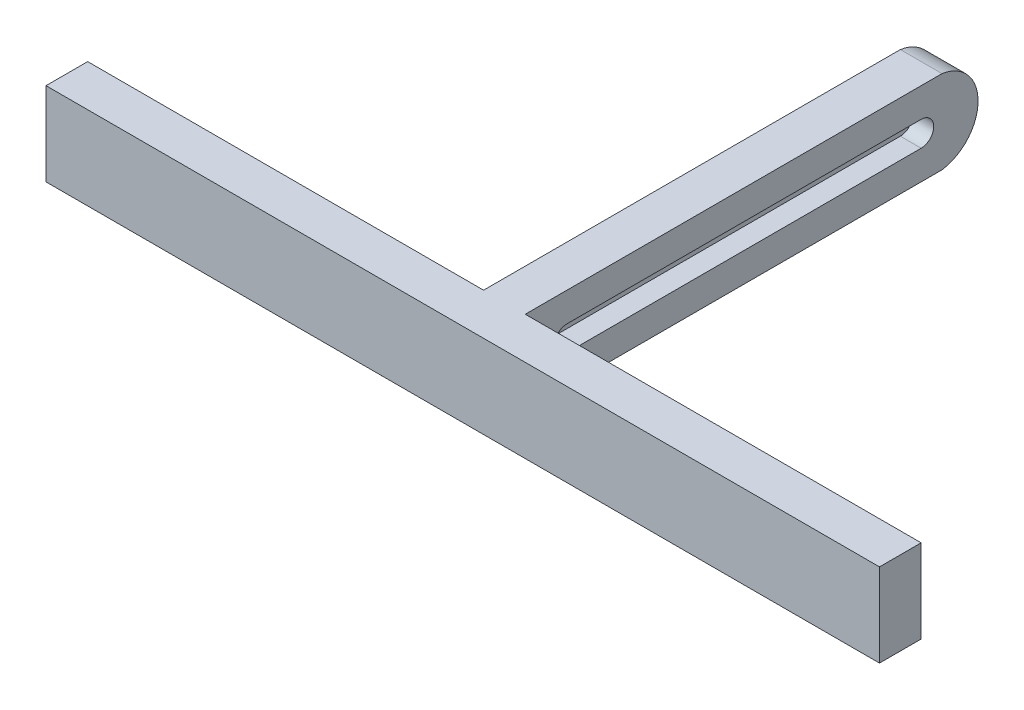
SolidWorks part; units mm, degrees
other "Main"
ref_plane "Front Plane" through (0, 0, 0) normal (0, 0, 1) x (1, 0, 0)
ref_plane "Top Plane" through (0, 0, 0) normal (0, 1, 0) x (1, 0, 0)
ref_plane "Right Plane" through (0, 0, 0) normal (1, 0, 0) x (0, 0, -1)
sketch "Sketch1" plane through (0, 0, 0) normal (1, 0, 0) x (0, 0, -1)
  line L1 (-50, 10) -> (50, 10)
  line L2 (-50, 10) -> (-50, -10)
  line L3 (-50, -10) -> (50, -10)
  line L4 (50, 10) -> (50, -10)
extrude "Back" add sketch "Sketch1" along normal blind 10 from offset 5 offset against normal yes
sketch "Sketch5" plane through (0, 0, 0) normal (1, 0, 0) x (0, 0, -1)
  arc A0 (50, 10) -> (50, -10) centre (48.5551, 0) cw
extrude "Curve End" add sketch "Sketch5" along normal blind 10 from offset 5 thin offset against normal yes
sketch "Sketch7" plane through (0, 0, 0) normal (1, 0, 0) x (0, 0, -1)
  line L1 (-40, 3) -> (45, 3)
  line L3 (-40, -3) -> (45, -3)
  arc A0 (-40, 3) -> (-40, -3) centre (-40, 0) ccw
  arc A1 (45, 3) -> (45, -3) centre (45, 0) cw
extrude "Slot" cut sketch "Sketch7" against normal blind 5 from offset 5
sketch "Sketch11" plane through (0, 0, 0) normal (1, 0, 0) x (0, 0, -1)
  line L1 (-50, 10) -> (-60, 10)
  line L2 (-50, 10) -> (-50, -10)
  line L3 (-50, -10) -> (-60, -10)
  line L4 (-60, 10) -> (-60, -10)
extrude "Front" add sketch "Sketch11" along normal blind 200 from offset 100
